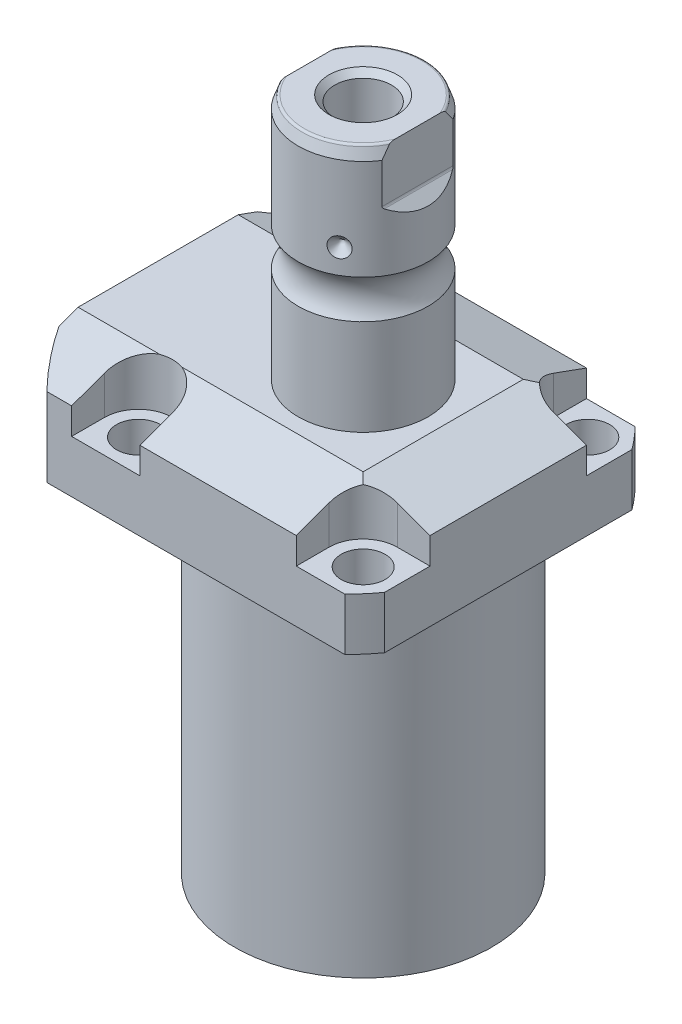
SolidWorks part; units mm, degrees
material "Alloy Steel"
ref_plane "Front Plane" through (0, 0, 0) normal (0, 0, 1) x (1, 0, 0)
ref_plane "Top Plane" through (0, 0, 0) normal (0, 1, 0) x (1, 0, 0)
ref_plane "Right Plane" through (0, 0, 0) normal (1, 0, 0) x (0, 0, -1)
sketch "Sketch1" plane through (0, 0, 0) normal (0, -1, 0) x (0, 0, 1)
  line L0 (-35.433, 50.063) -> (35.433, 50.063)
  line L1 (35.433, 50.063) -> (35.433, -35.433)
  line L2 (35.433, -35.433) -> (-35.433, -35.433)
  line L3 (-35.433, -35.433) -> (-35.433, 50.063)
  line L4 (0, 0) -> (0, -60.6467) construction
  dimension "D1" = 35.433
  dimension "D2" = 85.496
  dimension "D3" = 70.866
extrude "Extrude1" add sketch "Sketch1" against normal blind 104.4448
sketch "Sketch2" plane through (0, 0, 0) normal (0, -1, 0) x (1, 0, 0)
  circle A0 centre (-5.4102, 0) radius 50.8
  dimension "D1" = 101.6
  dimension "D2" = 5.4102
extrude "Cut-Extrude1" cut sketch "Sketch2" against normal through all flip side to cut
sketch "Sketch3" plane through (0, 0, 0) normal (1, 0, 0) x (0, 0, -1)
  line L0 (31.3945, 0) -> (31.3945, 79.4258)
  line L1 (31.3945, 79.4258) -> (76.5937, 79.4258)
  line L2 (76.5937, 79.4258) -> (76.5937, 0)
  line L3 (76.5937, 0) -> (31.3945, 0)
  line L4 (0, -93.345) -> (0, 4.445) construction
  line L5 (24.2233, 0) -> (-24.2233, 0) construction
  dimension "D1" = 62.789
  dimension "D2" = 153.1874
  dimension "D3" = 79.4258
revolve "Cut-Revolve1" cut sketch "Sketch3" angle 360 about L4
fillet "Fillet1" radius 0.381 1 edges at (0, 79.4258, -31.3945)
sketch "Sketch4" plane through (0, 104.4448, 0) normal (0, 1, 0) x (-1, 0, 0)
  line L0 (-35.433, -30.2072) -> (-35.433, 30.2072) construction
  line L1 (41.8127, 35.433) -> (-30.9923, 35.433) construction
  line L2 (-19.1008, -35.433) -> (-19.1008, -27.432)
  line L3 (-35.433, -35.433) -> (-19.1008, -35.433)
  line L4 (-35.433, -19.1008) -> (-35.433, -35.433)
  line L5 (-27.432, -19.1008) -> (-35.433, -19.1008)
  line L6 (35.7632, -35.433) -> (19.1008, -35.433)
  line L7 (19.1008, 35.433) -> (19.1008, 27.432)
  line L8 (35.7632, 35.433) -> (35.7632, 27.432)
  line L9 (35.7632, 35.433) -> (19.1008, 35.433)
  line L10 (-27.432, 19.1008) -> (-35.433, 19.1008)
  line L11 (-35.433, 19.1008) -> (-35.433, 35.433)
  line L12 (-35.433, 35.433) -> (-19.1008, 35.433)
  line L13 (-19.1008, 35.433) -> (-19.1008, 27.432)
  line L14 (-48.9217, 0) -> (49.4551, 0) construction
  line L15 (35.7632, -35.433) -> (35.7632, -27.432)
  line L16 (19.1008, -35.433) -> (19.1008, -27.432)
  arc A0 (19.1008, -27.432) -> (35.7632, -27.432) centre (27.432, -27.432) cw
  arc A1 (-27.432, -19.1008) -> (-19.1008, -27.432) centre (-27.432, -27.432) cw
  arc A2 (-27.432, 19.1008) -> (-19.1008, 27.432) centre (-27.432, 27.432) ccw
  arc A3 (19.1008, 27.432) -> (35.7632, 27.432) centre (27.432, 27.432) ccw
  dimension "D2" = 8.3312
  dimension "D1" = 27.432
  dimension "D3" = 27.432
  dimension "D4" = 54.864
extrude "Cut-Extrude2" cut sketch "Sketch4" against normal blind 12.243
sketch "Sketch5" plane through (0, 0, 0) normal (1, 0, 0) x (0, 0, -1)
  line L0 (-19.558, 104.4448) -> (-35.433, 98.6668)
  line L1 (0, 0) -> (0, 154.1081) construction
  line L2 (-19.558, 104.4448) -> (-35.433, 104.4448)
  line L3 (-35.433, 104.4448) -> (-35.433, 98.6668)
  dimension "D1" = 15.875
  dimension "D2" = 20
extrude "Cut-Extrude9" cut sketch "Sketch5" against normal through all and the other way through all
mirror "Mirror1" about plane through (0, 0, 0) normal (0, 0, 1) of "Cut-Extrude9"
sketch "Sketch9" plane through (0, 0, 0) normal (0, 0, 1) x (1, 0, 0)
  line L0 (19.558, 104.4448) -> (35.433, 98.6668)
  line L1 (35.433, 98.6668) -> (35.433, 104.4448)
  line L2 (35.433, 104.4448) -> (19.558, 104.4448)
  dimension "D1" = 15.875
  dimension "D2" = 20
extrude "Cut-Extrude7" cut sketch "Sketch9" against normal through all and the other way through all
ref_plane "Plane14" through (-35.0774, 0, 0) normal (1, 0, 0) x (0, 0, -1)
sketch "Sketch20" plane through (-35.0774, 88.9, -18.1102) normal (1, 0, 0) x (0, 1, 0)
  line L0 (-88.9, 18.1102) -> (39.8401, 18.1102) construction
  line L1 (-7.2797, 32.639) -> (36.9042, 32.639) construction
  line L2 (-9.4742, 38.3413) -> (-8.0264, 38.3413)
  line L3 (-9.4742, -6.1131) -> (-9.4742, 42.3335) construction
  line L4 (-8.0264, 38.3413) -> (-8.0264, 35.8902)
  line L5 (-8.0264, 35.8902) -> (-7.0104, 35.8902)
  line L6 (-7.0104, 35.8902) -> (-7.0104, 33.8836)
  line L7 (-7.0104, 33.8836) -> (3.9624, 33.8836)
  line L8 (3.9624, 33.8836) -> (3.9624, 32.639)
  line L9 (3.9624, 32.639) -> (-9.4742, 32.639)
  line L10 (-9.4742, 38.3413) -> (-9.4742, 32.639)
  dimension "D1" = 14.5288
  dimension "D2" = 11.4046
  dimension "D3" = 1.4478
  dimension "D4" = 6.5024
  dimension "D5" = 1.016
  dimension "D6" = 2.4892
  dimension "D7" = 10.9728
revolve "Cut-Revolve4" cut sketch "Sketch20" angle 360 about L1
mirror "Mirror10" about plane through (0, 0, 0) normal (0, 0, 1) of "Cut-Revolve4"
sketch "Sketch10" plane through (-35.0774, 88.9, -18.1102) normal (1, 0, 0) x (0, 1, 0)
  line L0 (-1.0325, 3.5814) -> (1.5659, 3.5814) construction
  line L1 (3.9624, 4.826) -> (-7.0104, 4.826) construction
  line L2 (-7.0104, 2.3368) -> (3.9624, 2.3368) construction
  line L4 (-9.4742, -12.097) -> (-9.4742, 48.3174) construction
  circle A0 centre (-9.2075, 8.1026) radius 1.1811
  dimension "D1" = 2.3622
  dimension "D2" = 0.2667
  dimension "D3" = 9.0424
revolve "Revolve4" add sketch "Sketch10" angle 360 about L0
mirror "Mirror12" about plane through (0, 0, 0) normal (0, 0, 1) of bodies 135
sketch "Sketch15" plane through (0, 0, 0) normal (1, 0, 0) x (0, 0, -1)
  line L0 (0, 104.4448) -> (15.875, 104.4448)
  line L1 (15.875, 104.4448) -> (15.875, 127.8297)
  line L2 (15.875, 137.2439) -> (15.875, 161.7218)
  line L3 (14.8118, 164.6428) -> (0, 164.6428)
  line L4 (0, 164.6428) -> (0, 104.4448)
  line L5 (0, 250.2908) -> (0, 28.9095) construction
  line L6 (19.558, 104.4448) -> (-19.558, 104.4448) construction
  line L7 (14.8118, 164.6428) -> (15.875, 161.7218)
  line L9 (24.2233, 79.4258) -> (35.433, 79.4258) construction
  arc A0 (15.875, 137.2439) -> (15.875, 127.8297) centre (22.2504, 132.5368) ccw
  dimension "D2" = 20
  dimension "D4" = 7.9248
  dimension "D6" = 28.6512
  dimension "D1" = 85.217
  dimension "D3" = 31.75
  dimension "D5" = 32.106
  dimension "D7" = 2.921
revolve "Revolve3" add sketch "Sketch15" angle 360 about L5
hole_wizard "Hole1" positions "Sketch18" profile "Sketch17" legacy end condition up to next
sketch "Sketch18" plane through (0, 92.2018, 0) normal (0, 1, 0) x (-1, 0, 0)
  arc A0 (35.7632, -27.432) -> (19.1008, -27.432) centre (27.432, -27.432) ccw construction
  arc A1 (19.1008, 27.432) -> (35.7632, 27.432) centre (27.432, 27.432) ccw construction
  arc A2 (-27.432, 19.1008) -> (-19.1008, 27.432) centre (-27.432, 27.432) ccw construction
  arc A3 (-19.1008, -27.432) -> (-27.432, -19.1008) centre (-27.432, -27.432) ccw construction
  point P0 (-27.432, -27.432)
  point P1 (-27.432, 27.432)
  point P3 (27.432, 27.432)
  point P5 (27.432, -27.432)
sketch "Sketch17" plane through (27.432, 92.2018, -27.432) normal (1, 0, 0) x (0, 0, 1)
  line L0 (0, 0) -> (0, 12.776)
  line L1 (0, 12.776) -> (5.3594, 12.776)
  line L2 (5.3594, 12.776) -> (5.3594, 0)
  line L3 (5.3594, 0) -> (0, 0)
  line L4 (0, 110) -> (0, -10) construction
  dimension "Diameter" = 10.7188
  dimension "Depth" = 12.776
chamfer "Chamfer1" distance 0.635 angle 45 2 edges at (-35.0774, 81.8896, 13.2842) (-35.0774, 81.8896, -13.2842)
ref_plane "Plane15" through (0, 91.9226, 0) normal (0, -1, 0) x (1, 0, 0)
sketch "Sketch21" plane through (0, 91.9226, 0) normal (0, -1, 0) x (1, 0, 0)
  line L0 (-57.5495, -12.9794) -> (-2.9353, -12.9794) construction
  line L1 (-50.063, -1.9304) -> (-49.809, -1.9304)
  line L2 (-49.809, -1.9304) -> (-49.809, -6.7564)
  line L3 (-49.809, -6.7564) -> (-47.2563, -7.4404)
  line L4 (-46.6957, -8.001) -> (-30.759, -8.001)
  line L5 (-30.759, -8.001) -> (-30.759, -12.9794)
  line L6 (-30.759, -12.9794) -> (-50.063, -12.9794)
  line L7 (-50.063, 24.2233) -> (-50.063, -24.2233) construction
  line L8 (-50.063, -12.9794) -> (-50.063, -1.9304)
  line L9 (-47.2563, -7.4404) -> (-46.6957, -8.001)
  dimension "D1" = 12.9794
  dimension "D2" = 0.254
  dimension "D3" = 22.098
  dimension "D4" = 45
  dimension "D5" = 2.5527
  dimension "D6" = 9.9568
  dimension "D7" = 19.05
  dimension "D8" = 15
  dimension "D9" = 12.446
revolve "Cut-Revolve5" cut sketch "Sketch21" angle 360 about L0
mirror "Mirror13" about plane through (0, 0, 0) normal (0, 0, 1) of "Cut-Revolve5"
fillet "Fillet2" radius 0.635 1 edges at (0, 164.6428, 14.8118)
sketch "Sketch26" plane through (0, 0, 0) normal (0, 0, 1) x (1, 0, 0)
  line L0 (-39.772, 143.2048) -> (35.3173, 143.2048) construction
  line L1 (-15.875, 145.6178) -> (-13.462, 143.2048)
  line L2 (-15.875, 161.7218) -> (-15.875, 137.2439) construction
  line L3 (-13.462, 143.2048) -> (-15.875, 143.2048)
  line L4 (-15.875, 143.2048) -> (-15.875, 145.6178)
  arc A0 (-15.875, 127.8297) -> (-15.875, 137.2439) centre (-22.2504, 132.5368) ccw construction
  dimension "D1" = 45
  dimension "D2" = 4.826
  dimension "D3" = 10.668
revolve "Cut-Revolve7" cut sketch "Sketch26" angle 360 about L0
pattern_circular "CirPattern1" count 3 over 360 about axis through (0, 250.2908, 0) along (0, 1, 0) of "Cut-Revolve7"
hole_wizard "Hole2" positions "Sketch28" profile "Sketch27" legacy
sketch "Sketch28" plane through (0, 164.6428, 0) normal (0, 1, 0) x (-1, 0, 0)
  circle A0 centre (0, 0) radius 15.875 construction
  point P0 (0, 0)
sketch "Sketch27" plane through (0, 164.6428, 0) normal (1, 0, 0) x (0, 0, 1)
  line L0 (0, 0) -> (0, 28.8121)
  line L1 (0, 28.8121) -> (6.9469, 24.638)
  line L2 (6.9469, 24.638) -> (6.9469, 0)
  line L4 (6.9469, 0) -> (0, 0)
  line L6 (0, 28.8121) -> (-6.9469, 24.638) construction
  line L7 (0, -4.2442) -> (0, 117.3081) construction
  dimension "Diameter" = 13.8938
  dimension "Depth" = 24.638
  dimension "Drill Angle" = 118
sketch "Sketch29" plane through (0, 0, 0) normal (0, 0, 1) x (1, 0, 0)
  line L0 (0, 0) -> (0, 192.0172) construction
  line L1 (13.284, 164.6428) -> (13.284, 151.9428)
  line L2 (14.3672, 164.6428) -> (-14.3672, 164.6428) construction
  line L3 (13.5072, 151.404) -> (16.332, 148.5792)
  line L5 (16.332, 148.5792) -> (16.332, 164.6428)
  line L6 (16.332, 164.6428) -> (13.284, 164.6428)
  line L7 (-16.332, 164.6428) -> (-13.284, 164.6428)
  line L8 (-16.332, 148.5792) -> (-16.332, 164.6428)
  line L9 (-13.5072, 151.404) -> (-16.332, 148.5792)
  line L10 (-13.284, 164.6428) -> (-13.284, 151.9428)
  arc A0 (13.284, 151.9428) -> (13.5072, 151.404) centre (14.046, 151.9428) ccw
  arc A1 (-13.284, 151.9428) -> (-13.5072, 151.404) centre (-14.046, 151.9428) cw
  dimension "D2" = 0.762
  dimension "D1" = 45
  dimension "D3" = 26.568
  dimension "D4" = 12.7
  dimension "D5" = 3.048
extrude "Cut-Extrude10" cut sketch "Sketch29" against normal through all and the other way through all
chamfer "Chamfer2" distance 1.4351 angle 45 1 edges at (0, 164.6428, 6.9469)
